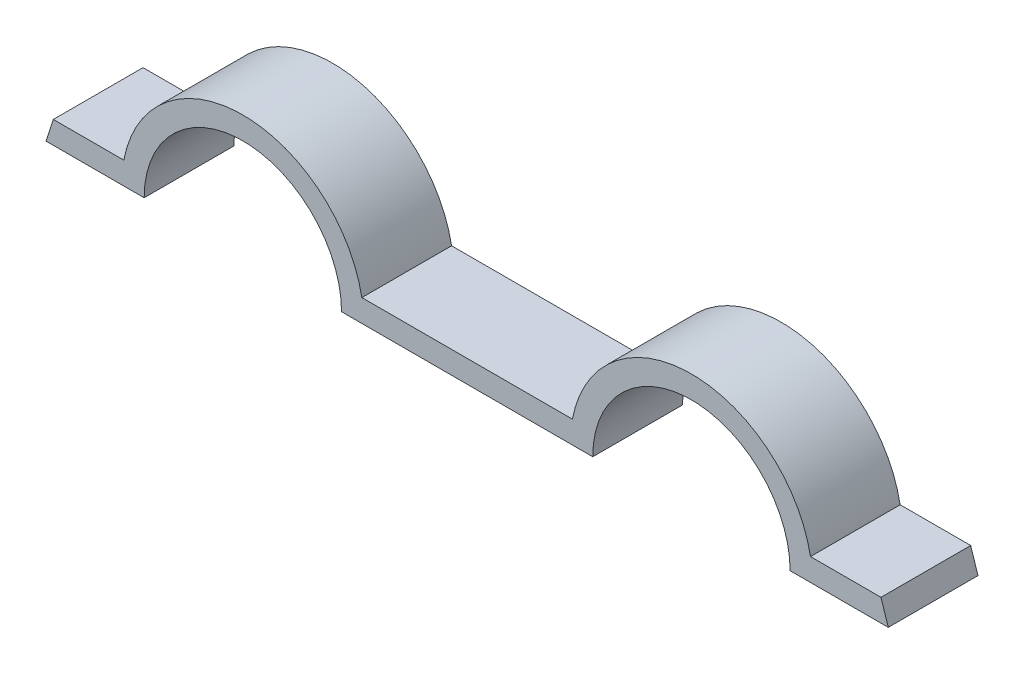
SolidWorks part; units mm, degrees
ref_plane "Front Plane" through (0, 0, 0) normal (0, 0, 1) x (1, 0, 0)
ref_plane "Top Plane" through (0, 0, 0) normal (0, 1, 0) x (1, 0, 0)
ref_plane "Right Plane" through (0, 0, 0) normal (1, 0, 0) x (0, 0, -1)
sketch "Sketch1" plane through (0, 0, 0) normal (0, 0, 1) x (1, 0, 0)
  line L0 (0, 0) -> (0, 324.652) construction
  line L1 (30.7076, 181.3003) -> (24.6961, 151.9943) construction
  line L2 (37.137, 149.4423) -> (40.6988, 166.8059) construction
  line L3 (-37.137, 149.4423) -> (-40.6988, 166.8059) construction
  line L4 (-30.7076, 181.3003) -> (-24.6961, 151.9943) construction
  line L5 (0, 0) -> (-38.8975, 189.6253) construction
  line L6 (27.6276, 178.6698) -> (37.137, 149.4423) construction
  line L7 (0, 0) -> (38.8975, 189.6253) construction
  line L12 (30.2004, 175.8931) -> (45.4337, 129.0731) construction
  line L13 (-27.6276, 178.6698) -> (-37.137, 149.4423) construction
  line L14 (-30.2004, 175.8931) -> (-45.4337, 129.0731) construction
  line L47 (-29.8065, 171.9727) -> (-22.86, 171.9727)
  line L50 (-8.89, 171.9727) -> (8.89, 171.9727)
  line L51 (-29.29, 173.5602) -> (-24.2992, 173.5602)
  line L52 (-29.29, 173.5602) -> (-29.8065, 171.9727)
  line L53 (-7.4508, 173.5602) -> (7.4508, 173.5602)
  line L54 (29.29, 173.5602) -> (29.8065, 171.9727)
  line L55 (29.29, 173.5602) -> (24.2992, 173.5602)
  line L56 (29.8065, 171.9727) -> (22.86, 171.9727)
  circle A0 centre (0, 0) radius 152.4 construction
  circle A1 centre (9.5123, 172.7758) radius 12.7 construction
  circle A2 centre (9.5123, 172.7758) radius 19.05 construction
  circle A3 centre (-15.875, 171.9727) radius 6.35 construction
  circle A4 centre (-15.875, 171.9727) radius 12.7 construction
  circle A5 centre (0, 0) radius 153.9875 construction
  circle A8 centre (0, 149.4423) radius 44.248 construction
  circle A10 centre (0, 149.4423) radius 45.8355 construction
  circle A38 centre (15.875, 171.9727) radius 12.7 construction
  circle A39 centre (15.875, 171.9727) radius 6.35 construction
  arc A45 (-8.89, 171.9727) -> (-22.86, 171.9727) centre (-15.875, 171.9727) ccw
  arc A46 (-7.4508, 173.5602) -> (-24.2992, 173.5602) centre (-15.875, 171.9727) ccw
  arc A47 (8.89, 171.9727) -> (22.86, 171.9727) centre (15.875, 171.9727) cw
  arc A48 (7.4508, 173.5602) -> (24.2992, 173.5602) centre (15.875, 171.9727) cw
  point P42 (0, 173.5602)
  point P47 (0, 171.9727)
  dimension "D1" = 304.8
  dimension "D2" = 25.4
  dimension "D3" = 15.875
  dimension "D4" = 38.1
  dimension "D5" = 12.7
  dimension "D6" = 9.5123
  dimension "D8" = 307.975
  dimension "D7" = 13.97
  dimension "D11" = 88.496
  dimension "D12" = 91.671
  dimension "D13" = 1.5875
  dimension "D14" = 17.145
  dimension "D9" = 6.35
  dimension "D10" = 6.35
  dimension "D15" = 1.5875
extrude "Boss-Extrude2" add sketch "Sketch1" along normal blind 6.35
